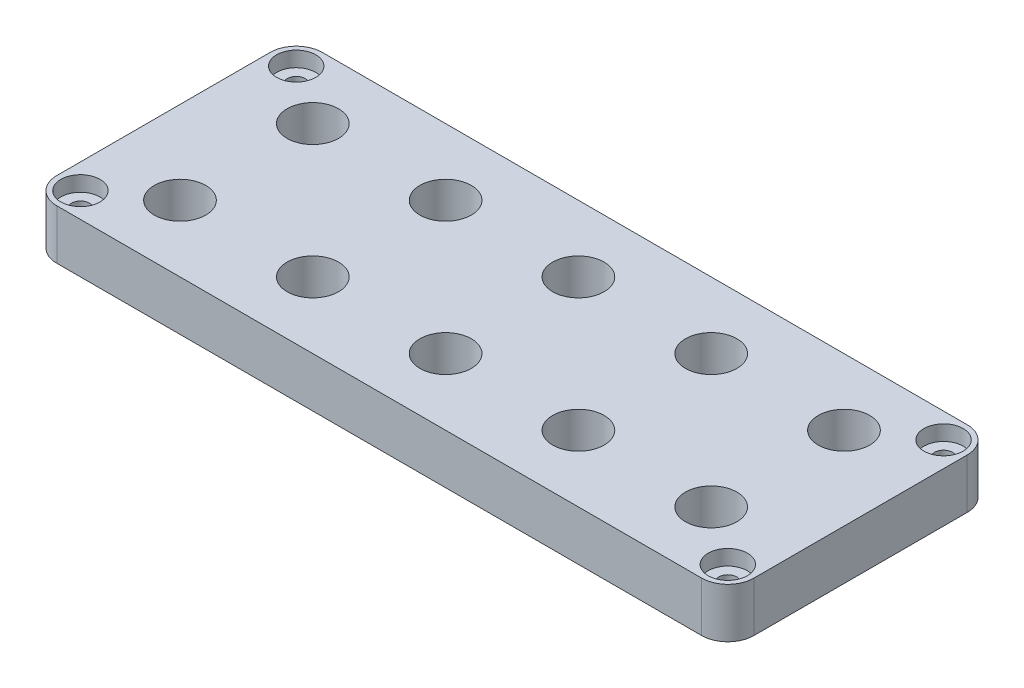
SolidWorks part; units mm, degrees
material "Acrylic (Medium-high impact)"
ref_plane "Front Plane" through (0, 0, 0) normal (0, 0, 1) x (1, 0, 0)
ref_plane "Top Plane" through (0, 0, 0) normal (0, 1, 0) x (1, 0, 0)
ref_plane "Right Plane" through (0, 0, 0) normal (1, 0, 0) x (0, 0, -1)
sketch "Sketch1" plane through (0, 0, 0) normal (0, 1, 0) x (1, 0, 0)
  line L0 (-35.8657, 50.8) -> (278.0629, 50.8) construction
  line L1 (0, 0) -> (266.7, 0)
  line L2 (0, 0) -> (0, 101.6)
  line L3 (0, 101.6) -> (266.7, 101.6)
  line L4 (266.7, 0) -> (266.7, 101.6)
  line L5 (133.35, 126.4872) -> (133.35, -69.7182) construction
  circle A0 centre (31.75, 25.4) radius 19.05 construction
  circle A1 centre (31.75, 25.4) radius 9.8425
  circle A2 centre (82.55, 25.4) radius 9.8425
  circle A3 centre (82.55, 25.4) radius 19.05 construction
  circle A4 centre (133.35, 25.4) radius 9.8425
  circle A5 centre (133.35, 25.4) radius 19.05 construction
  circle A6 centre (184.15, 25.4) radius 9.8425
  circle A7 centre (184.15, 25.4) radius 19.05 construction
  circle A8 centre (234.95, 25.4) radius 9.8425
  circle A9 centre (234.95, 25.4) radius 19.05 construction
  circle A10 centre (82.55, 76.2) radius 9.8425
  circle A11 centre (82.55, 76.2) radius 19.05 construction
  circle A12 centre (133.35, 76.2) radius 9.8425
  circle A13 centre (133.35, 76.2) radius 19.05 construction
  circle A14 centre (184.15, 76.2) radius 9.8425
  circle A15 centre (184.15, 76.2) radius 19.05 construction
  circle A16 centre (234.95, 76.2) radius 9.8425
  circle A17 centre (234.95, 76.2) radius 19.05 construction
  circle A18 centre (31.75, 76.2) radius 9.8425
  circle A19 centre (31.75, 76.2) radius 19.05 construction
  circle A20 centre (9.525, 92.075) radius 3.429
  circle A21 centre (257.175, 92.075) radius 3.429
  circle A22 centre (9.525, 92.075) radius 6.604 construction
  circle A23 centre (9.525, 9.525) radius 3.429
  circle A24 centre (257.175, 9.525) radius 3.429
  dimension "D1" = 31.75
  dimension "D7" = 9.525
  dimension "D2" = 25.4
  dimension "D5" = 266.7
  dimension "D6" = 101.6
  dimension "D8" = 9.525
  dimension "D3" = 5
  dimension "D4" = 2
extrude "Boss-Extrude1" add sketch "Sketch1" along normal blind 19.05
fillet "Fillet1" radius 10 4 edges at (266.7, 9.525, -101.6) (266.7, 9.525, 0) (0, 9.525, 0) (0, 9.525, -101.6)
sketch "Sketch2" plane through (0, 19.05, 0) normal (0, 1, 0) x (1, 0, 0)
  circle A0 centre (9.525, 92.075) radius 7.5
  circle A1 centre (257.175, 92.075) radius 7.5
  circle A2 centre (257.175, 9.525) radius 7.5
  circle A3 centre (9.525, 9.525) radius 7.5
  dimension "D1" = 2
  dimension "D2" = 2
extrude "Cut-Extrude1" cut sketch "Sketch2" against normal blind 5.842
